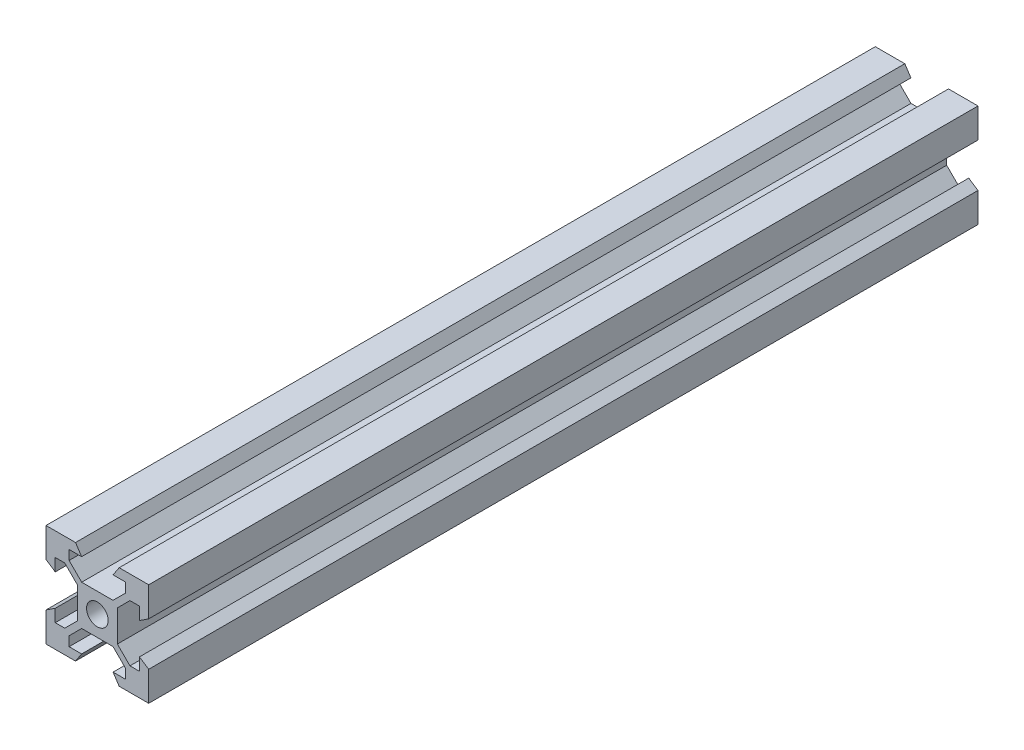
SolidWorks part; units mm, degrees
ref_plane "Front Plane" through (0, 0, 0) normal (0, 0, 1) x (1, 0, 0)
ref_plane "Top Plane" through (0, 0, 0) normal (0, 1, 0) x (1, 0, 0)
ref_plane "Right Plane" through (0, 0, 0) normal (1, 0, 0) x (0, 0, -1)
sketch "Sketch1" plane through (0, 0, 0) normal (0, 0, 1) x (1, 0, 0)
  line L0 (-10, 10) -> (-4.25, 10)
  line L1 (-4.25, 10) -> (-3.065, 8.2)
  line L2 (-3.065, 8.2) -> (-5.5, 8.2)
  line L3 (-5.5, 8.2) -> (-5.5, 6.3485)
  line L4 (-5.5, 6.3485) -> (-3.0515, 3.9)
  line L5 (-3.0515, 3.9) -> (0, 3.9)
  line L6 (-10, 10) -> (0, 0) construction
  line L7 (-3.9, 3.0515) -> (-3.9, 0)
  line L8 (-6.3485, 5.5) -> (-3.9, 3.0515)
  line L9 (-8.2, 3.065) -> (-8.2, 5.5)
  line L10 (-8.2, 5.5) -> (-6.3485, 5.5)
  line L11 (-10, 4.25) -> (-8.2, 3.065)
  line L12 (-10, 10) -> (-10, 4.25)
  line L13 (10, 10) -> (10, 4.25)
  line L14 (10, 10) -> (4.25, 10)
  line L15 (4.25, 10) -> (3.065, 8.2)
  line L16 (3.065, 8.2) -> (5.5, 8.2)
  line L17 (5.5, 8.2) -> (5.5, 6.3485)
  line L18 (8.2, 5.5) -> (6.3485, 5.5)
  line L19 (8.2, 3.065) -> (8.2, 5.5)
  line L20 (10, 4.25) -> (8.2, 3.065)
  line L21 (3.9, 3.0515) -> (3.9, 0)
  line L22 (6.3485, 5.5) -> (3.9, 3.0515)
  line L23 (5.5, 6.3485) -> (3.0515, 3.9)
  line L24 (3.0515, 3.9) -> (0, 3.9)
  line L25 (10, -10) -> (4.25, -10)
  line L26 (10, -10) -> (10, -4.25)
  line L27 (10, -4.25) -> (8.2, -3.065)
  line L28 (8.2, -3.065) -> (8.2, -5.5)
  line L29 (8.2, -5.5) -> (6.3485, -5.5)
  line L30 (5.5, -8.2) -> (5.5, -6.3485)
  line L31 (3.065, -8.2) -> (5.5, -8.2)
  line L32 (4.25, -10) -> (3.065, -8.2)
  line L33 (3.0515, -3.9) -> (0, -3.9)
  line L34 (5.5, -6.3485) -> (3.0515, -3.9)
  line L35 (6.3485, -5.5) -> (3.9, -3.0515)
  line L36 (3.9, -3.0515) -> (3.9, 0)
  line L37 (-10, -10) -> (-10, -4.25)
  line L38 (-10, -10) -> (-4.25, -10)
  line L39 (-4.25, -10) -> (-3.065, -8.2)
  line L40 (-3.065, -8.2) -> (-5.5, -8.2)
  line L41 (-5.5, -8.2) -> (-5.5, -6.3485)
  line L42 (-8.2, -5.5) -> (-6.3485, -5.5)
  line L43 (-8.2, -3.065) -> (-8.2, -5.5)
  line L44 (-10, -4.25) -> (-8.2, -3.065)
  line L45 (-3.9, -3.0515) -> (-3.9, 0)
  line L46 (-6.3485, -5.5) -> (-3.9, -3.0515)
  line L47 (-5.5, -6.3485) -> (-3.0515, -3.9)
  line L48 (-3.0515, -3.9) -> (0, -3.9)
  circle A0 centre (0, 0) radius 2.1
  point P58 (0, 0)
  dimension "D1" = 4.2
  dimension "D2" = 10
  dimension "D3" = 10
  dimension "D4" = 6.1
  dimension "D5" = 4.3
  dimension "D6" = 3.065
  dimension "D7" = 5.5
  dimension "D8" = 1.2
  dimension "D9" = 4.25
  dimension "D10" = 4
extrude "Boss-Extrude1" add sketch "Sketch1" along normal blind 161.5
ref_plane "Plane1" through (0, 0, 80.75) normal (0, 0, 1) x (1, 0, 0)
